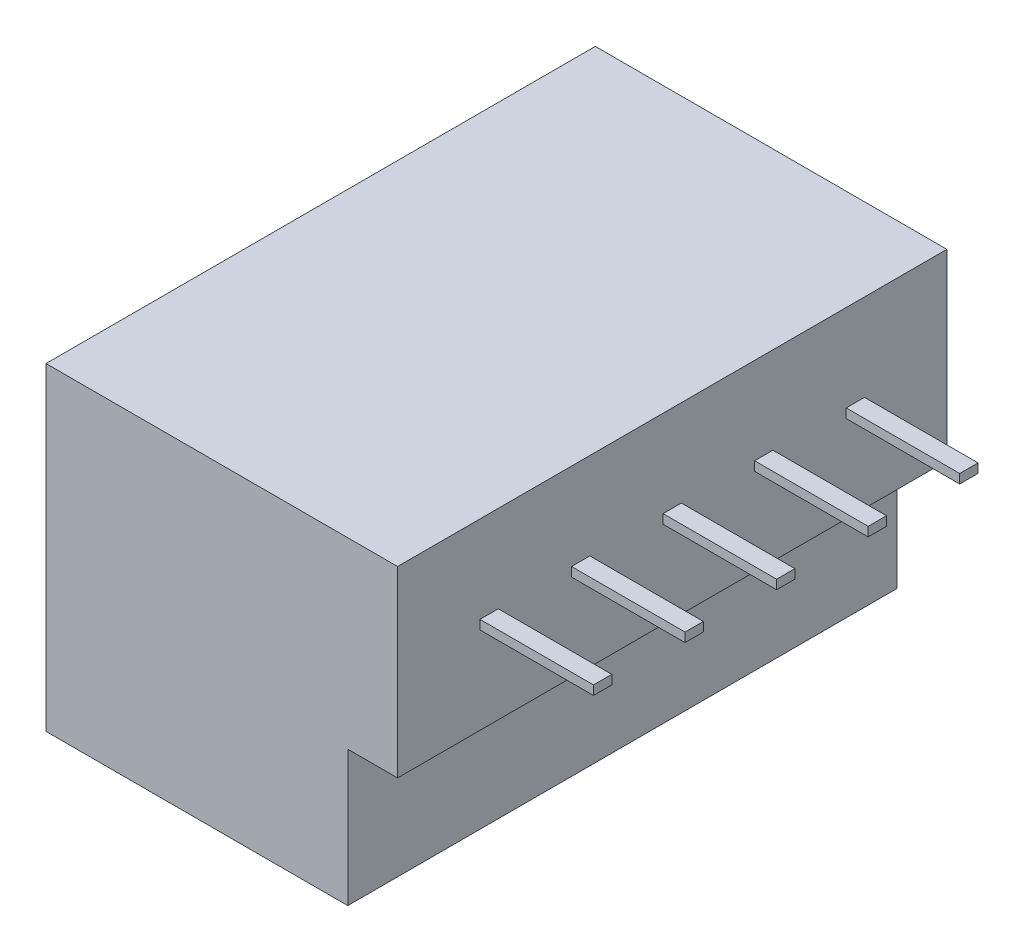
SolidWorks part; units mm, degrees
ref_plane "Front Plane" through (0, 0, 0) normal (0, 0, 1) x (1, 0, 0)
ref_plane "Top Plane" through (0, 0, 0) normal (0, 1, 0) x (1, 0, 0)
ref_plane "Right Plane" through (0, 0, 0) normal (1, 0, 0) x (0, 0, -1)
sketch "Sketch1" plane through (0, 0, 0) normal (0, 1, 0) x (1, 0, 0)
  line L1 (-20.3569, 6.7781) -> (-12.1169, 6.7781)
  line L2 (-20.3569, 6.7781) -> (-20.3569, -8.2219)
  line L3 (-20.3569, -8.2219) -> (-12.1169, -8.2219)
  line L4 (-12.1169, 6.7781) -> (-12.1169, -8.2219)
  dimension "D1" = 15
  dimension "D2" = 8.24
extrude "Boss-Extrude1" add sketch "Sketch1" along normal blind 3.7
sketch "Sketch2" plane through (0, 3.7, 0) normal (0, 1, 0) x (1, 0, 0)
  line L1 (-20.3569, -8.2219) -> (-12.1169, -8.2219)
  line L2 (-20.3569, -8.2219) -> (-20.3569, 6.7781)
  line L3 (-20.3569, 6.7781) -> (-12.1169, 6.7781)
  line L5 (-12.1169, 6.7781) -> (-10.7569, 6.7781)
  line L7 (-12.1169, -8.2219) -> (-10.7569, -8.2219)
  line L8 (-10.7569, 6.7781) -> (-10.7569, -8.2219)
  dimension "D1" = 1.36
extrude "Boss-Extrude2" add sketch "Sketch2" along normal blind 5
sketch "Sketch3" plane through (-10.7569, 0, 0) normal (1, 0, 0) x (0, 0, -1)
  line L0 (-8.2219, 8.7) -> (6.7781, 8.7) construction
  line L1 (-5.9719, 6.325) -> (-5.4719, 6.325)
  line L2 (-5.9719, 6.325) -> (-5.9719, 6.075)
  line L3 (-5.9719, 6.075) -> (-5.4719, 6.075)
  line L4 (-5.4719, 6.325) -> (-5.4719, 6.075)
  line L5 (-8.2219, 3.7) -> (6.7781, 3.7) construction
  line L6 (6.7781, 8.7) -> (6.7781, 3.7) construction
  line L7 (-3.4719, 6.325) -> (-2.9719, 6.325)
  line L8 (-3.4719, 6.325) -> (-3.4719, 6.075)
  line L9 (-3.4719, 6.075) -> (-2.9719, 6.075)
  line L10 (-2.9719, 6.325) -> (-2.9719, 6.075)
  line L11 (-0.9719, 6.325) -> (-0.4719, 6.325)
  line L12 (-0.9719, 6.325) -> (-0.9719, 6.075)
  line L13 (-0.9719, 6.075) -> (-0.4719, 6.075)
  line L14 (-0.4719, 6.325) -> (-0.4719, 6.075)
  line L15 (1.5281, 6.325) -> (2.0281, 6.325)
  line L16 (1.5281, 6.325) -> (1.5281, 6.075)
  line L17 (1.5281, 6.075) -> (2.0281, 6.075)
  line L18 (2.0281, 6.325) -> (2.0281, 6.075)
  line L19 (4.0281, 6.325) -> (4.5281, 6.325)
  line L20 (4.0281, 6.325) -> (4.0281, 6.075)
  line L21 (4.0281, 6.075) -> (4.5281, 6.075)
  line L22 (4.5281, 6.325) -> (4.5281, 6.075)
  line L23 (-8.2219, 8.7) -> (-8.2219, 3.7) construction
  dimension "D1" = 0.5
  dimension "D2" = 0.25
  dimension "D3" = 2.375
  dimension "D4" = 2.375
  dimension "D5" = 0.5
  dimension "D6" = 0.5
  dimension "D7" = 0.5
  dimension "D8" = 0.5
  dimension "D9" = 2.25
  dimension "D10" = 2
  dimension "D11" = 2
  dimension "D12" = 2
  dimension "D13" = 2.25
extrude "Boss-Extrude3" add sketch "Sketch3" along normal blind 3.1
